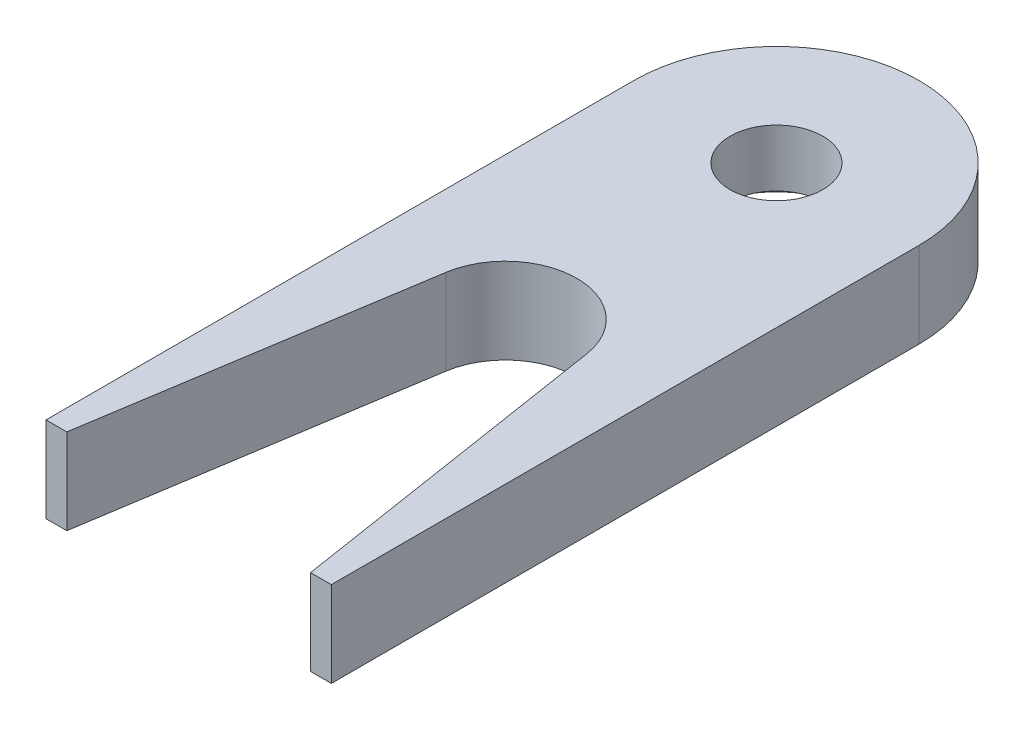
SolidWorks part; units mm, degrees
ref_plane "Спереди" through (0, 0, 0) normal (0, 0, 1) x (1, 0, 0)
ref_plane "Сверху" through (0, 0, 0) normal (0, 1, 0) x (1, 0, 0)
ref_plane "Справа" through (0, 0, 0) normal (1, 0, 0) x (0, 0, -1)
sketch "Эскиз1" plane through (0, 0, 0) normal (0, 1, 0) x (1, 0, 0)
  line L0 (0, 0) -> (0, -32.3333) construction
  line L1 (-13.7902, -14) -> (12.4514, -14) construction
  line L2 (-4.9396, -18.2255) -> (-8.542, -41.1995)
  line L3 (4.9396, -18.2255) -> (8.542, -41.1995)
  line L4 (-10, 0) -> (-10, -41.1995)
  line L5 (-10, -41.1995) -> (-8.542, -41.1995)
  line L6 (10, -41.1995) -> (8.542, -41.1995)
  line L7 (10, 0) -> (10, -41.1995)
  circle A0 centre (0, 0) radius 3.25
  circle A1 centre (0, 0) radius 10 construction
  arc A2 (-4.9396, -18.2255) -> (4.9396, -18.2255) centre (0, -19) cw
  arc A3 (-10, 0) -> (10, 0) centre (0, 0) cw
  point P10 (0, -14)
  dimension "D1" = 6.5
  dimension "D2" = 20
  dimension "D4" = 5
  dimension "D3" = 14
extrude "Бобышка-Вытянуть1" add sketch "Эскиз1" along normal blind 6
sketch "Эскиз2" plane through (0, 0, 0) normal (0, -1, 0) x (1, 0, 0)
  circle A0 centre (0, 0) radius 6
  dimension "D1" = 12
extrude "Вырез-Вытянуть1" cut sketch "Эскиз2" against normal blind 2
